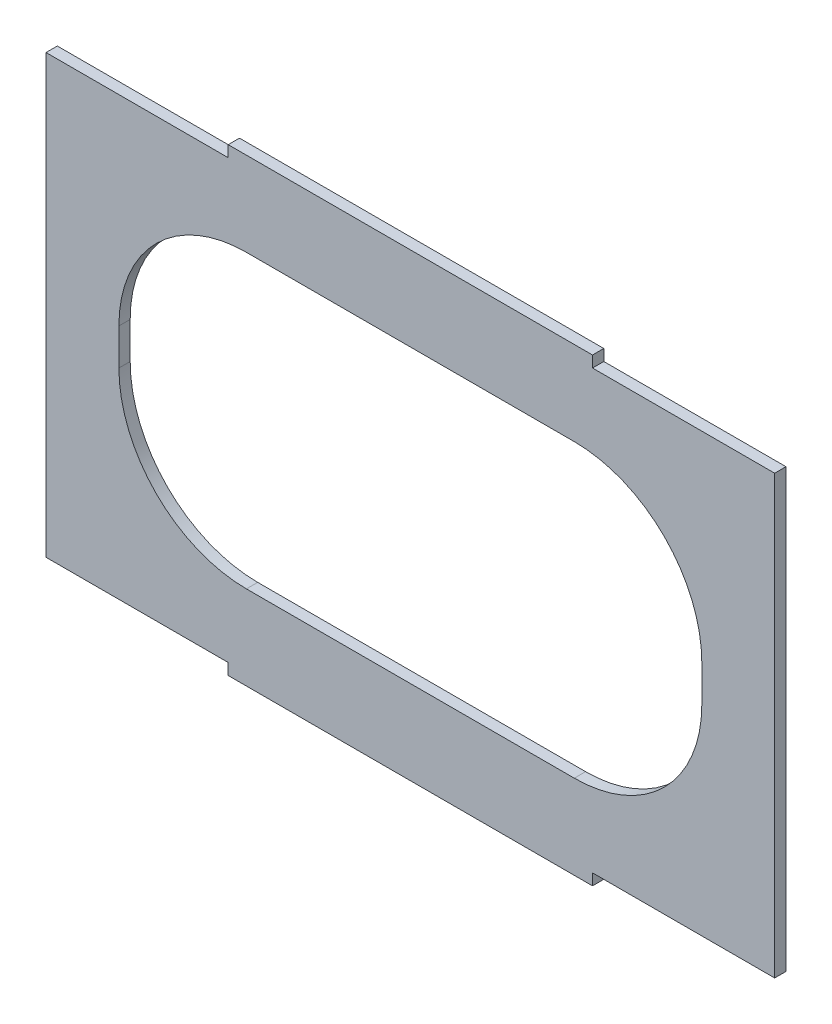
SolidWorks part; units mm, degrees
material "Teak"
ref_plane "Front Plane" through (0, 0, 0) normal (0, 0, 1) x (1, 0, 0)
ref_plane "Top Plane" through (0, 0, 0) normal (0, 1, 0) x (1, 0, 0)
ref_plane "Right Plane" through (0, 0, 0) normal (1, 0, 0) x (0, 0, -1)
sketch "Sketch1" plane through (0, 0, 0) normal (0, 0, 1) x (1, 0, 0)
  line L1 (-100, -60) -> (100, -60)
  line L2 (-100, -60) -> (-100, 60)
  line L3 (-100, 60) -> (100, 60)
  line L4 (100, -60) -> (100, 60)
  line L5 (-100, -60) -> (100, 60) construction
  line L6 (-100, 60) -> (100, -60) construction
  line L7 (-80, -40) -> (80, -40)
  line L8 (-80, -40) -> (-80, 40)
  line L9 (-80, 40) -> (80, 40)
  line L10 (80, -40) -> (80, 40)
  line L11 (-80, -40) -> (80, 40) construction
  line L12 (-80, 40) -> (80, -40) construction
  point P0 (0, 0)
  point P6 (0, 0)
  dimension "D1" = 200
  dimension "D2" = 120
  dimension "D3" = 20
  dimension "D4" = 20
extrude "Boss-Extrude1" add sketch "Sketch1" along normal blind 3.1
sketch "Sketch2" plane through (0, 0, 3.1) normal (0, 0, 1) x (1, 0, 0)
  line L0 (100, 60) -> (-100, 60) construction
  line L1 (-50, 63.1) -> (50, 63.1)
  line L2 (-50, 63.1) -> (-50, 60)
  line L3 (-50, 60) -> (50, 60)
  line L4 (50, 63.1) -> (50, 60)
  line L5 (-50, 63.1) -> (50, 60) construction
  line L6 (-50, 60) -> (50, 63.1) construction
  line L7 (-80, 0) -> (80, 0) construction
  line L8 (-80, 40) -> (-80, -40) construction
  line L9 (80, -40) -> (80, 40) construction
  line L10 (-50, -60) -> (50, -63.1) construction
  line L11 (-50, -63.1) -> (50, -60) construction
  line L12 (50, -63.1) -> (50, -60)
  line L13 (-50, -60) -> (50, -60)
  line L14 (-50, -63.1) -> (-50, -60)
  line L15 (-50, -63.1) -> (50, -63.1)
  point P0 (0, 61.55)
  point P18 (0, -61.55)
  dimension "D1" = 3.1
  dimension "D2" = 100
  dimension "D3" = 0
extrude "Boss-Extrude2" add sketch "Sketch2" against normal blind 3.1
fillet "Fillet1" radius 35 4 edges at (80, -40, 1.55) (80, 40, 1.55) (-80, -40, 1.55) (-80, 40, 1.55)
equation "\"thick\" = 3.1mm"
equation "\"small_bearing_outer\"=12.9mm"
equation "\"servo1_L\"=40.7mm"
equation "\"servo1_W\"=20.5mm"
equation "\"servo1_H\"=43.5mm"
equation "\"servo1_hL\"=49mm"
equation "\"servo1_hW\"=10mm"
equation "\"servo1_H2\"=27mm"
equation "\"large_bearing_inner\"=2.75in"
equation "\"large_bearing_outer\"=4.75in"
equation "\"large_bearing_thick\"=3/8in"
equation "\"large_bearing_h1\"=3.25in"
equation "\"large_bearing_h2\"=4.25in"
equation "\"D1@Sketch2\"=\"thick\""
